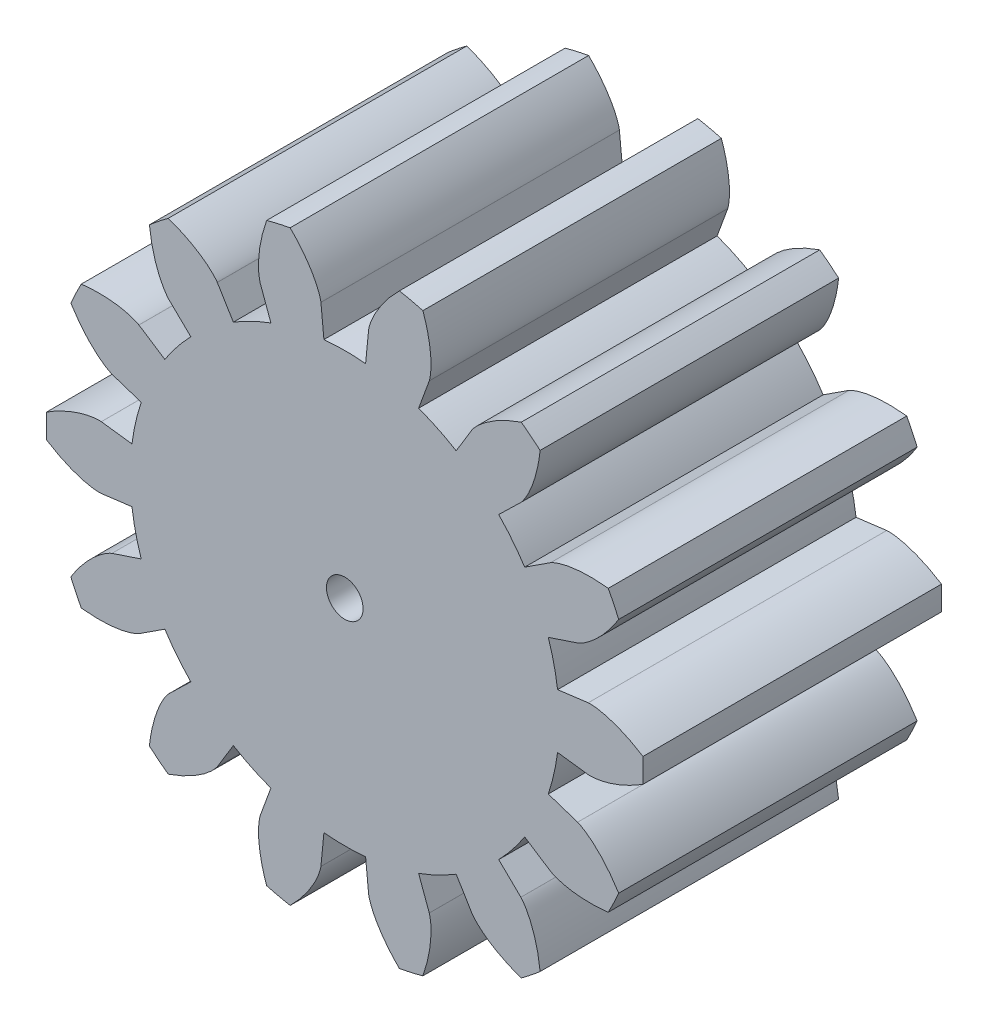
SolidWorks part; units mm, degrees
ref_plane "Front Plane" through (0, 0, 0) normal (0, 0, 1) x (1, 0, 0)
ref_plane "Top Plane" through (0, 0, 0) normal (0, 1, 0) x (1, 0, 0)
ref_plane "Right Plane" through (0, 0, 0) normal (1, 0, 0) x (0, 0, -1)
sketch "Sketch1" plane through (0, 0, 0) normal (0, 0, 1) x (1, 0, 0)
  line L0 (11.8001, -11.4535) -> (10.315, -10.012)
  line L1 (11.8013, -11.4547) -> (11.8001, -11.4535)
  line L2 (8.5406, -14.0529) -> (8.5414, -14.0543)
  line L3 (7.4657, -12.2843) -> (8.5406, -14.0529)
  line L4 (5.662, -15.4391) -> (4.9495, -13.4961)
  line L5 (5.6626, -15.4407) -> (5.662, -15.4391)
  line L6 (1.5975, -16.3668) -> (1.5976, -16.3685)
  line L7 (1.3964, -14.307) -> (1.5975, -16.3668)
  line L8 (-1.5975, -16.3668) -> (-1.3964, -14.307)
  line L9 (-1.5976, -16.3685) -> (-1.5975, -16.3668)
  line L10 (-5.662, -15.4391) -> (-5.6626, -15.4407)
  line L11 (-4.9495, -13.4961) -> (-5.662, -15.4391)
  line L12 (-8.5406, -14.0529) -> (-7.4657, -12.2843)
  line L13 (-8.5414, -14.0543) -> (-8.5406, -14.0529)
  line L14 (-11.8001, -11.4535) -> (-11.8013, -11.4547)
  line L15 (-10.315, -10.012) -> (-11.8001, -11.4535)
  line L16 (-13.7921, -8.9556) -> (-12.0563, -7.8285)
  line L17 (-13.7935, -8.9565) -> (-13.7921, -8.9556)
  line L18 (-15.601, -5.1994) -> (-15.6026, -5.1999)
  line L19 (-13.6376, -4.545) -> (-15.601, -5.1994)
  line L20 (-16.312, -2.0846) -> (-14.259, -1.8222)
  line L21 (-16.3136, -2.0847) -> (-16.312, -2.0846)
  line L22 (-16.312, 2.0846) -> (-16.3136, 2.0847)
  line L23 (-14.259, 1.8222) -> (-16.312, 2.0846)
  line L24 (-15.601, 5.1994) -> (-13.6376, 4.545)
  line L25 (-15.6026, 5.1999) -> (-15.601, 5.1994)
  line L26 (-13.7921, 8.9556) -> (-13.7935, 8.9565)
  line L27 (-12.0563, 7.8285) -> (-13.7921, 8.9556)
  line L28 (-11.8001, 11.4535) -> (-10.315, 10.012)
  line L29 (-11.8013, 11.4547) -> (-11.8001, 11.4535)
  line L30 (-8.5406, 14.0529) -> (-8.5414, 14.0543)
  line L31 (-7.4657, 12.2843) -> (-8.5406, 14.0529)
  line L32 (-5.662, 15.4391) -> (-4.9495, 13.4961)
  line L33 (-5.6626, 15.4407) -> (-5.662, 15.4391)
  line L34 (-1.5975, 16.3668) -> (-1.5976, 16.3685)
  line L35 (-1.3964, 14.307) -> (-1.5975, 16.3668)
  line L36 (1.5975, 16.3668) -> (1.3964, 14.307)
  line L37 (1.5976, 16.3685) -> (1.5975, 16.3668)
  line L38 (5.662, 15.4391) -> (5.6626, 15.4407)
  line L39 (4.9495, 13.4961) -> (5.662, 15.4391)
  line L40 (8.5406, 14.0529) -> (7.4657, 12.2843)
  line L41 (8.5414, 14.0543) -> (8.5406, 14.0529)
  line L42 (11.8001, 11.4535) -> (11.8013, 11.4547)
  line L43 (10.315, 10.012) -> (11.8001, 11.4535)
  line L44 (13.7921, 8.9556) -> (12.0563, 7.8285)
  line L45 (13.7935, 8.9565) -> (13.7921, 8.9556)
  line L46 (15.601, 5.1994) -> (15.6026, 5.1999)
  line L47 (13.6376, 4.545) -> (15.601, 5.1994)
  line L48 (16.312, 2.0846) -> (14.259, 1.8222)
  line L49 (16.3136, 2.0847) -> (16.312, 2.0846)
  line L50 (16.312, -2.0846) -> (16.3136, -2.0847)
  line L51 (14.259, -1.8222) -> (16.312, -2.0846)
  line L52 (15.601, -5.1994) -> (13.6376, -4.545)
  line L53 (15.6026, -5.1999) -> (15.601, -5.1994)
  line L54 (13.7921, -8.9556) -> (13.7935, -8.9565)
  line L55 (12.0563, -7.8285) -> (13.7921, -8.9556)
  arc A0 (10.315, -10.012) -> (12.0563, -7.8285) centre (0, 0) ccw
  arc A1 (11.8285, -16.1272) -> (13.0908, -15.1206) centre (0, 0) ccw
  arc A2 (4.9495, -13.4961) -> (7.4657, -12.2843) centre (0, 0) ccw
  arc A3 (3.6598, -19.6623) -> (5.2338, -19.303) centre (0, 0) ccw
  arc A4 (-1.3964, -14.307) -> (1.3964, -14.307) centre (0, 0) ccw
  arc A5 (-5.2338, -19.303) -> (-3.6598, -19.6623) centre (0, 0) ccw
  arc A6 (-7.4657, -12.2843) -> (-4.9495, -13.4961) centre (0, 0) ccw
  arc A7 (-13.0908, -15.1206) -> (-11.8285, -16.1272) centre (0, 0) ccw
  arc A8 (-12.0563, -7.8285) -> (-10.315, -10.012) centre (0, 0) ccw
  arc A9 (-18.3549, -7.9433) -> (-17.6544, -9.3979) centre (0, 0) ccw
  arc A10 (-14.259, -1.8222) -> (-13.6376, -4.545) centre (0, 0) ccw
  arc A11 (-19.9837, 0.8073) -> (-19.9837, -0.8073) centre (0, 0) ccw
  arc A12 (-13.6376, 4.545) -> (-14.259, 1.8222) centre (0, 0) ccw
  arc A13 (-17.6544, 9.3979) -> (-18.3549, 7.9433) centre (0, 0) ccw
  arc A14 (-10.315, 10.012) -> (-12.0563, 7.8285) centre (0, 0) ccw
  arc A15 (-11.8285, 16.1272) -> (-13.0908, 15.1206) centre (0, 0) ccw
  arc A16 (-4.9495, 13.4961) -> (-7.4657, 12.2843) centre (0, 0) ccw
  arc A17 (-3.6598, 19.6623) -> (-5.2338, 19.303) centre (0, 0) ccw
  arc A18 (1.3964, 14.307) -> (-1.3964, 14.307) centre (0, 0) ccw
  arc A19 (5.2338, 19.303) -> (3.6598, 19.6623) centre (0, 0) ccw
  arc A20 (7.4657, 12.2843) -> (4.9495, 13.4961) centre (0, 0) ccw
  arc A21 (13.0908, 15.1206) -> (11.8285, 16.1272) centre (0, 0) ccw
  arc A22 (12.0563, 7.8285) -> (10.315, 10.012) centre (0, 0) ccw
  arc A23 (18.3549, 7.9433) -> (17.6544, 9.3979) centre (0, 0) ccw
  arc A24 (14.259, 1.8222) -> (13.6376, 4.545) centre (0, 0) ccw
  arc A25 (19.9837, -0.8073) -> (19.9837, 0.8073) centre (0, 0) ccw
  arc A26 (13.6376, -4.545) -> (14.259, -1.8222) centre (0, 0) ccw
  arc A27 (17.6544, -9.3979) -> (18.3549, -7.9433) centre (0, 0) ccw
  circle A28 centre (0, 0) radius 1.2268
  spline S0 degree 5 poles (13.0908, -15.1206) (13.0892, -15.1057) (13.0837, -15.0564) (13.0741, -14.9729) (13.0534, -14.8076) (13.0196, -14.5739) (12.9712, -14.2913) (12.9095, -13.9876) (12.8326, -13.6678) (12.7526, -13.3794) (12.6689, -13.1136) (12.5842, -12.8734) (12.5, -12.6578) (12.4177, -12.4654) (12.3382, -12.2951) (12.264, -12.1481) (12.1946, -12.0199) (12.1305, -11.9094) (12.0722, -11.8149) (12.02, -11.7352) (11.9742, -11.669) (11.9347, -11.6148) (11.9014, -11.5712) (11.8749, -11.5382) (11.8529, -11.5117) (11.836, -11.4921) (11.824, -11.4787) (11.8135, -11.4673) (11.8071, -11.4606) (11.8039, -11.4573) (11.8022, -11.4556) (11.8013, -11.4547) knots 0 0 0 0 0 0 0.0125 0.041667 0.070833 0.141667 0.204167 0.266667 0.325 0.383333 0.4375 0.491667 0.541667 0.5875 0.633333 0.675 0.7125 0.75 0.783333 0.816667 0.845833 0.870833 0.895833 0.916667 0.933333 0.954167 0.966667 0.975 1 1 1 1 1 1 weights 1 1 1 1 1 1 1 1 1 1 1 1 1 1 1 1 1 1 1 1 1 1 1 1 1 1 1 1 1 1 1 1
  spline S1 degree 5 poles (8.5414, -14.0543) (8.5418, -14.0548) (8.5426, -14.0561) (8.5443, -14.0588) (8.5474, -14.0636) (8.5539, -14.0732) (8.5633, -14.0868) (8.5824, -14.1133) (8.6247, -14.1691) (8.699, -14.2586) (8.8131, -14.3827) (8.9784, -14.5426) (9.1766, -14.7141) (9.3765, -14.8717) (9.593, -15.028) (9.8169, -15.1767) (10.0477, -15.3185) (10.2796, -15.4503) (10.5206, -15.5776) (10.7579, -15.694) (10.9807, -15.7959) (11.237, -15.9058) (11.4544, -15.992) (11.6185, -16.0533) (11.7392, -16.0964) (11.8285, -16.1272) knots 0 0 0 0 0 0 0.0125 0.025 0.0375 0.05 0.075 0.095833 0.158333 0.258333 0.325 0.395833 0.4625 0.525 0.583333 0.641667 0.695833 0.75 0.795833 0.85 0.891667 0.920833 1 1 1 1 1 1 weights 1 1 1 1 1 1 1 1 1 1 1 1 1 1 1 1 1 1 1 1 1 1 1 1 1 1
  spline S2 degree 5 poles (5.2338, -19.303) (5.2388, -19.289) (5.2553, -19.2421) (5.2828, -19.1628) (5.3359, -19.0048) (5.4069, -18.7797) (5.4859, -18.504) (5.5621, -18.2036) (5.6315, -17.8821) (5.6845, -17.5876) (5.7245, -17.3118) (5.7524, -17.0587) (5.7701, -16.8279) (5.7794, -16.6188) (5.7817, -16.4308) (5.7787, -16.2662) (5.7717, -16.1206) (5.7619, -15.9932) (5.7504, -15.8827) (5.738, -15.7883) (5.7254, -15.7088) (5.7133, -15.6428) (5.7022, -15.5891) (5.6927, -15.5479) (5.6844, -15.5145) (5.6776, -15.4895) (5.6726, -15.4722) (5.6681, -15.4574) (5.6653, -15.4486) (5.6638, -15.4442) (5.663, -15.4419) (5.6626, -15.4407) knots 0 0 0 0 0 0 0.0125 0.041667 0.070833 0.141667 0.204167 0.266667 0.325 0.383333 0.4375 0.491667 0.541667 0.5875 0.633333 0.675 0.7125 0.75 0.783333 0.816667 0.845833 0.870833 0.895833 0.916667 0.933333 0.954167 0.966667 0.975 1 1 1 1 1 1 weights 1 1 1 1 1 1 1 1 1 1 1 1 1 1 1 1 1 1 1 1 1 1 1 1 1 1 1 1 1 1 1 1
  spline S3 degree 5 poles (1.5976, -16.3685) (1.5977, -16.3691) (1.5979, -16.3706) (1.5983, -16.3737) (1.599, -16.3795) (1.6006, -16.3909) (1.6032, -16.4072) (1.6089, -16.4394) (1.6229, -16.508) (1.6509, -16.621) (1.6999, -16.7823) (1.7795, -16.998) (1.8836, -17.2385) (1.9953, -17.4672) (2.1226, -17.702) (2.2598, -17.9331) (2.4063, -18.161) (2.558, -18.3804) (2.7199, -18.5996) (2.8831, -18.8075) (3.0397, -18.9959) (3.2229, -19.2061) (3.3814, -19.3782) (3.5027, -19.5046) (3.5927, -19.5957) (3.6598, -19.6623) knots 0 0 0 0 0 0 0.0125 0.025 0.0375 0.05 0.075 0.095833 0.158333 0.258333 0.325 0.395833 0.4625 0.525 0.583333 0.641667 0.695833 0.75 0.795833 0.85 0.891667 0.920833 1 1 1 1 1 1 weights 1 1 1 1 1 1 1 1 1 1 1 1 1 1 1 1 1 1 1 1 1 1 1 1 1 1
  spline S4 degree 5 poles (-3.6598, -19.6623) (-3.6492, -19.6518) (-3.614, -19.6168) (-3.5548, -19.5572) (-3.4384, -19.4379) (-3.2768, -19.2658) (-3.086, -19.0518) (-2.887, -18.8142) (-2.6849, -18.5546) (-2.5094, -18.3123) (-2.3537, -18.0811) (-2.2187, -17.8652) (-2.1026, -17.6649) (-2.0036, -17.4806) (-1.9199, -17.3122) (-1.8512, -17.1626) (-1.7944, -17.0284) (-1.7479, -16.9094) (-1.7104, -16.8049) (-1.6806, -16.7144) (-1.6574, -16.6373) (-1.6396, -16.5726) (-1.6264, -16.5194) (-1.617, -16.4781) (-1.61, -16.4444) (-1.6053, -16.419) (-1.6023, -16.4013) (-1.5999, -16.3859) (-1.5986, -16.3767) (-1.5981, -16.3721) (-1.5978, -16.3697) (-1.5976, -16.3685) knots 0 0 0 0 0 0 0.0125 0.041667 0.070833 0.141667 0.204167 0.266667 0.325 0.383333 0.4375 0.491667 0.541667 0.5875 0.633333 0.675 0.7125 0.75 0.783333 0.816667 0.845833 0.870833 0.895833 0.916667 0.933333 0.954167 0.966667 0.975 1 1 1 1 1 1 weights 1 1 1 1 1 1 1 1 1 1 1 1 1 1 1 1 1 1 1 1 1 1 1 1 1 1 1 1 1 1 1 1
  spline S5 degree 5 poles (-5.6626, -15.4407) (-5.6628, -15.4413) (-5.6633, -15.4427) (-5.6643, -15.4457) (-5.6661, -15.4512) (-5.6696, -15.4622) (-5.6744, -15.478) (-5.6832, -15.5095) (-5.7004, -15.5773) (-5.7241, -15.6913) (-5.75, -15.8579) (-5.7719, -16.0868) (-5.7824, -16.3486) (-5.781, -16.6032) (-5.7682, -16.8699) (-5.7449, -17.1377) (-5.7118, -17.4065) (-5.6703, -17.67) (-5.6196, -17.9378) (-5.5627, -18.1959) (-5.5034, -18.4336) (-5.4295, -18.7025) (-5.3613, -18.9263) (-5.3069, -19.0928) (-5.2654, -19.214) (-5.2338, -19.303) knots 0 0 0 0 0 0 0.0125 0.025 0.0375 0.05 0.075 0.095833 0.158333 0.258333 0.325 0.395833 0.4625 0.525 0.583333 0.641667 0.695833 0.75 0.795833 0.85 0.891667 0.920833 1 1 1 1 1 1 weights 1 1 1 1 1 1 1 1 1 1 1 1 1 1 1 1 1 1 1 1 1 1 1 1 1 1
  spline S6 degree 5 poles (-11.8285, -16.1272) (-11.8144, -16.1223) (-11.7675, -16.106) (-11.6883, -16.0781) (-11.5317, -16.0211) (-11.3114, -15.9362) (-11.0466, -15.8261) (-10.7643, -15.6984) (-10.4696, -15.5522) (-10.2063, -15.41) (-9.9657, -15.2693) (-9.7504, -15.1333) (-9.5589, -15.0033) (-9.3897, -14.8801) (-9.2413, -14.7647) (-9.1145, -14.6597) (-9.005, -14.5635) (-8.9115, -14.4764) (-8.8323, -14.3985) (-8.7663, -14.33) (-8.7119, -14.2705) (-8.6678, -14.22) (-8.6328, -14.1778) (-8.6064, -14.1447) (-8.5855, -14.1173) (-8.5702, -14.0965) (-8.5599, -14.0818) (-8.551, -14.069) (-8.5459, -14.0613) (-8.5434, -14.0574) (-8.5421, -14.0554) (-8.5414, -14.0543) knots 0 0 0 0 0 0 0.0125 0.041667 0.070833 0.141667 0.204167 0.266667 0.325 0.383333 0.4375 0.491667 0.541667 0.5875 0.633333 0.675 0.7125 0.75 0.783333 0.816667 0.845833 0.870833 0.895833 0.916667 0.933333 0.954167 0.966667 0.975 1 1 1 1 1 1 weights 1 1 1 1 1 1 1 1 1 1 1 1 1 1 1 1 1 1 1 1 1 1 1 1 1 1 1 1 1 1 1 1
  spline S7 degree 5 poles (-11.8013, -11.4547) (-11.8017, -11.4551) (-11.8028, -11.4562) (-11.805, -11.4584) (-11.809, -11.4626) (-11.8169, -11.471) (-11.8281, -11.4832) (-11.8497, -11.5077) (-11.8946, -11.5614) (-11.9654, -11.6537) (-12.061, -11.7926) (-12.1801, -11.9894) (-12.3032, -12.2207) (-12.4124, -12.4507) (-12.5165, -12.6965) (-12.6117, -12.9479) (-12.6986, -13.2045) (-12.7755, -13.4598) (-12.8459, -13.7231) (-12.9067, -13.9804) (-12.9564, -14.2203) (-13.0065, -14.4946) (-13.0422, -14.7258) (-13.0654, -14.8994) (-13.0806, -15.0266) (-13.0908, -15.1206) knots 0 0 0 0 0 0 0.0125 0.025 0.0375 0.05 0.075 0.095833 0.158333 0.258333 0.325 0.395833 0.4625 0.525 0.583333 0.641667 0.695833 0.75 0.795833 0.85 0.891667 0.920833 1 1 1 1 1 1 weights 1 1 1 1 1 1 1 1 1 1 1 1 1 1 1 1 1 1 1 1 1 1 1 1 1 1
  spline S8 degree 5 poles (-17.6544, -9.3979) (-17.6396, -9.3996) (-17.5903, -9.4053) (-17.5068, -9.4145) (-17.341, -9.4311) (-17.1057, -9.4502) (-16.8194, -9.4659) (-16.5096, -9.4733) (-16.1806, -9.4695) (-15.8817, -9.4556) (-15.6039, -9.4332) (-15.3509, -9.4041) (-15.122, -9.37) (-14.9161, -9.3325) (-14.7323, -9.2929) (-14.5725, -9.2533) (-14.4321, -9.2141) (-14.3101, -9.1763) (-14.205, -9.1404) (-14.1157, -9.1073) (-14.0409, -9.0774) (-13.9793, -9.0509) (-13.9294, -9.0281) (-13.8913, -9.0097) (-13.8606, -8.9941) (-13.8377, -8.982) (-13.822, -8.9733) (-13.8085, -8.9656) (-13.8006, -8.9609) (-13.7966, -8.9584) (-13.7946, -8.9572) (-13.7935, -8.9565) knots 0 0 0 0 0 0 0.0125 0.041667 0.070833 0.141667 0.204167 0.266667 0.325 0.383333 0.4375 0.491667 0.541667 0.5875 0.633333 0.675 0.7125 0.75 0.783333 0.816667 0.845833 0.870833 0.895833 0.916667 0.933333 0.954167 0.966667 0.975 1 1 1 1 1 1 weights 1 1 1 1 1 1 1 1 1 1 1 1 1 1 1 1 1 1 1 1 1 1 1 1 1 1 1 1 1 1 1 1
  spline S9 degree 5 poles (-15.6026, -5.1999) (-15.6032, -5.2001) (-15.6046, -5.2006) (-15.6076, -5.2017) (-15.613, -5.2037) (-15.6237, -5.2078) (-15.6391, -5.214) (-15.6692, -5.2267) (-15.733, -5.2556) (-15.8369, -5.308) (-15.9832, -5.3917) (-16.1759, -5.5173) (-16.3871, -5.6723) (-16.5853, -5.8321) (-16.7858, -6.0084) (-16.9807, -6.1936) (-17.1702, -6.3872) (-17.3503, -6.5838) (-17.528, -6.7905) (-17.6944, -6.9959) (-17.8433, -7.1905) (-18.0074, -7.4159) (-18.1399, -7.6087) (-18.2362, -7.755) (-18.305, -7.8631) (-18.3549, -7.9433) knots 0 0 0 0 0 0 0.0125 0.025 0.0375 0.05 0.075 0.095833 0.158333 0.258333 0.325 0.395833 0.4625 0.525 0.583333 0.641667 0.695833 0.75 0.795833 0.85 0.891667 0.920833 1 1 1 1 1 1 weights 1 1 1 1 1 1 1 1 1 1 1 1 1 1 1 1 1 1 1 1 1 1 1 1 1 1
  spline S10 degree 5 poles (-19.9837, -0.8073) (-19.9711, -0.8152) (-19.9291, -0.8418) (-19.8578, -0.8863) (-19.7157, -0.9732) (-19.512, -1.0924) (-19.2608, -1.2308) (-18.9849, -1.3719) (-18.6868, -1.5112) (-18.4116, -1.6284) (-18.1516, -1.7287) (-17.911, -1.8123) (-17.6899, -1.8809) (-17.4881, -1.9364) (-17.3054, -1.9805) (-17.1442, -2.0142) (-17.0007, -2.0398) (-16.8744, -2.0586) (-16.7641, -2.0719) (-16.6693, -2.0809) (-16.5889, -2.0863) (-16.5219, -2.0892) (-16.4671, -2.0903) (-16.4248, -2.0903) (-16.3904, -2.0896) (-16.3645, -2.0885) (-16.3466, -2.0875) (-16.3311, -2.0864) (-16.3219, -2.0856) (-16.3173, -2.0852) (-16.3149, -2.0849) (-16.3136, -2.0847) knots 0 0 0 0 0 0 0.0125 0.041667 0.070833 0.141667 0.204167 0.266667 0.325 0.383333 0.4375 0.491667 0.541667 0.5875 0.633333 0.675 0.7125 0.75 0.783333 0.816667 0.845833 0.870833 0.895833 0.916667 0.933333 0.954167 0.966667 0.975 1 1 1 1 1 1 weights 1 1 1 1 1 1 1 1 1 1 1 1 1 1 1 1 1 1 1 1 1 1 1 1 1 1 1 1 1 1 1 1
  spline S11 degree 5 poles (-16.3136, 2.0847) (-16.3142, 2.0848) (-16.3158, 2.085) (-16.3189, 2.0853) (-16.3246, 2.0859) (-16.3361, 2.0868) (-16.3526, 2.0879) (-16.3852, 2.0895) (-16.4552, 2.0912) (-16.5716, 2.089) (-16.7398, 2.0771) (-16.9678, 2.0475) (-17.2254, 1.9995) (-17.4733, 1.9415) (-17.7305, 1.8697) (-17.9864, 1.7874) (-18.2411, 1.6953) (-18.4887, 1.5962) (-18.7385, 1.4871) (-18.9775, 1.3742) (-19.196, 1.2635) (-19.4418, 1.1317) (-19.6448, 1.0154) (-19.795, 0.9253) (-19.9039, 0.8579) (-19.9837, 0.8073) knots 0 0 0 0 0 0 0.0125 0.025 0.0375 0.05 0.075 0.095833 0.158333 0.258333 0.325 0.395833 0.4625 0.525 0.583333 0.641667 0.695833 0.75 0.795833 0.85 0.891667 0.920833 1 1 1 1 1 1 weights 1 1 1 1 1 1 1 1 1 1 1 1 1 1 1 1 1 1 1 1 1 1 1 1 1 1
  spline S12 degree 5 poles (-18.3549, 7.9433) (-18.3471, 7.9306) (-18.3207, 7.8885) (-18.2758, 7.8175) (-18.1854, 7.6775) (-18.0536, 7.4817) (-17.8874, 7.248) (-17.7001, 7.0012) (-17.4919, 6.7464) (-17.2948, 6.5213) (-17.104, 6.3181) (-16.9236, 6.1385) (-16.7542, 5.9807) (-16.5965, 5.8431) (-16.4509, 5.7241) (-16.3204, 5.6239) (-16.2022, 5.5385) (-16.0965, 5.4668) (-16.0029, 5.4069) (-15.9214, 5.3577) (-15.8513, 5.318) (-15.7922, 5.2863) (-15.7433, 5.2615) (-15.7052, 5.2432) (-15.6738, 5.2289) (-15.6501, 5.2186) (-15.6335, 5.2117) (-15.6191, 5.206) (-15.6104, 5.2027) (-15.606, 5.2011) (-15.6038, 5.2003) (-15.6026, 5.1999) knots 0 0 0 0 0 0 0.0125 0.041667 0.070833 0.141667 0.204167 0.266667 0.325 0.383333 0.4375 0.491667 0.541667 0.5875 0.633333 0.675 0.7125 0.75 0.783333 0.816667 0.845833 0.870833 0.895833 0.916667 0.933333 0.954167 0.966667 0.975 1 1 1 1 1 1 weights 1 1 1 1 1 1 1 1 1 1 1 1 1 1 1 1 1 1 1 1 1 1 1 1 1 1 1 1 1 1 1 1
  spline S13 degree 5 poles (-13.7935, 8.9565) (-13.794, 8.9568) (-13.7953, 8.9577) (-13.798, 8.9593) (-13.8029, 8.9623) (-13.8129, 8.9681) (-13.8273, 8.9763) (-13.856, 8.9919) (-13.9183, 9.0238) (-14.0241, 9.0722) (-14.1808, 9.1345) (-14.3991, 9.2068) (-14.652, 9.2753) (-14.9005, 9.3306) (-15.1634, 9.3775) (-15.4296, 9.4144) (-15.6991, 9.4419) (-15.9652, 9.4601) (-16.2376, 9.4702) (-16.5019, 9.4722) (-16.7468, 9.4672) (-17.0254, 9.4551) (-17.2588, 9.4384) (-17.4332, 9.4224) (-17.5606, 9.4089) (-17.6544, 9.3979) knots 0 0 0 0 0 0 0.0125 0.025 0.0375 0.05 0.075 0.095833 0.158333 0.258333 0.325 0.395833 0.4625 0.525 0.583333 0.641667 0.695833 0.75 0.795833 0.85 0.891667 0.920833 1 1 1 1 1 1 weights 1 1 1 1 1 1 1 1 1 1 1 1 1 1 1 1 1 1 1 1 1 1 1 1 1 1
  spline S14 degree 5 poles (-13.0908, 15.1206) (-13.0892, 15.1057) (-13.0837, 15.0564) (-13.0741, 14.9729) (-13.0534, 14.8076) (-13.0196, 14.5739) (-12.9712, 14.2913) (-12.9095, 13.9876) (-12.8326, 13.6678) (-12.7526, 13.3794) (-12.6689, 13.1136) (-12.5842, 12.8734) (-12.5, 12.6578) (-12.4177, 12.4654) (-12.3382, 12.2951) (-12.264, 12.1481) (-12.1946, 12.0199) (-12.1305, 11.9094) (-12.0722, 11.8149) (-12.02, 11.7352) (-11.9742, 11.669) (-11.9347, 11.6148) (-11.9014, 11.5712) (-11.8749, 11.5382) (-11.8529, 11.5117) (-11.836, 11.4921) (-11.824, 11.4787) (-11.8135, 11.4673) (-11.8071, 11.4606) (-11.8039, 11.4573) (-11.8022, 11.4556) (-11.8013, 11.4547) knots 0 0 0 0 0 0 0.0125 0.041667 0.070833 0.141667 0.204167 0.266667 0.325 0.383333 0.4375 0.491667 0.541667 0.5875 0.633333 0.675 0.7125 0.75 0.783333 0.816667 0.845833 0.870833 0.895833 0.916667 0.933333 0.954167 0.966667 0.975 1 1 1 1 1 1 weights 1 1 1 1 1 1 1 1 1 1 1 1 1 1 1 1 1 1 1 1 1 1 1 1 1 1 1 1 1 1 1 1
  spline S15 degree 5 poles (-8.5414, 14.0543) (-8.5418, 14.0548) (-8.5426, 14.0561) (-8.5443, 14.0588) (-8.5474, 14.0636) (-8.5539, 14.0732) (-8.5633, 14.0868) (-8.5824, 14.1133) (-8.6247, 14.1691) (-8.699, 14.2586) (-8.8131, 14.3827) (-8.9784, 14.5426) (-9.1766, 14.7141) (-9.3765, 14.8717) (-9.593, 15.028) (-9.8169, 15.1767) (-10.0477, 15.3185) (-10.2796, 15.4503) (-10.5206, 15.5776) (-10.7579, 15.694) (-10.9807, 15.7959) (-11.237, 15.9058) (-11.4544, 15.992) (-11.6185, 16.0533) (-11.7392, 16.0964) (-11.8285, 16.1272) knots 0 0 0 0 0 0 0.0125 0.025 0.0375 0.05 0.075 0.095833 0.158333 0.258333 0.325 0.395833 0.4625 0.525 0.583333 0.641667 0.695833 0.75 0.795833 0.85 0.891667 0.920833 1 1 1 1 1 1 weights 1 1 1 1 1 1 1 1 1 1 1 1 1 1 1 1 1 1 1 1 1 1 1 1 1 1
  spline S16 degree 5 poles (-5.2338, 19.303) (-5.2388, 19.289) (-5.2553, 19.2421) (-5.2828, 19.1628) (-5.3359, 19.0048) (-5.4069, 18.7797) (-5.4859, 18.504) (-5.5621, 18.2036) (-5.6315, 17.8821) (-5.6845, 17.5876) (-5.7245, 17.3118) (-5.7524, 17.0587) (-5.7701, 16.8279) (-5.7794, 16.6188) (-5.7817, 16.4308) (-5.7787, 16.2662) (-5.7717, 16.1206) (-5.7619, 15.9932) (-5.7504, 15.8827) (-5.738, 15.7883) (-5.7254, 15.7088) (-5.7133, 15.6428) (-5.7022, 15.5891) (-5.6927, 15.5479) (-5.6844, 15.5145) (-5.6776, 15.4895) (-5.6726, 15.4722) (-5.6681, 15.4574) (-5.6653, 15.4486) (-5.6638, 15.4442) (-5.663, 15.4419) (-5.6626, 15.4407) knots 0 0 0 0 0 0 0.0125 0.041667 0.070833 0.141667 0.204167 0.266667 0.325 0.383333 0.4375 0.491667 0.541667 0.5875 0.633333 0.675 0.7125 0.75 0.783333 0.816667 0.845833 0.870833 0.895833 0.916667 0.933333 0.954167 0.966667 0.975 1 1 1 1 1 1 weights 1 1 1 1 1 1 1 1 1 1 1 1 1 1 1 1 1 1 1 1 1 1 1 1 1 1 1 1 1 1 1 1
  spline S17 degree 5 poles (-1.5976, 16.3685) (-1.5977, 16.3691) (-1.5979, 16.3706) (-1.5983, 16.3737) (-1.599, 16.3795) (-1.6006, 16.3909) (-1.6032, 16.4072) (-1.6089, 16.4394) (-1.6229, 16.508) (-1.6509, 16.621) (-1.6999, 16.7823) (-1.7795, 16.998) (-1.8836, 17.2385) (-1.9953, 17.4672) (-2.1226, 17.702) (-2.2598, 17.9331) (-2.4063, 18.161) (-2.558, 18.3804) (-2.7199, 18.5996) (-2.8831, 18.8075) (-3.0397, 18.9959) (-3.2229, 19.2061) (-3.3814, 19.3782) (-3.5027, 19.5046) (-3.5927, 19.5957) (-3.6598, 19.6623) knots 0 0 0 0 0 0 0.0125 0.025 0.0375 0.05 0.075 0.095833 0.158333 0.258333 0.325 0.395833 0.4625 0.525 0.583333 0.641667 0.695833 0.75 0.795833 0.85 0.891667 0.920833 1 1 1 1 1 1 weights 1 1 1 1 1 1 1 1 1 1 1 1 1 1 1 1 1 1 1 1 1 1 1 1 1 1
  spline S18 degree 5 poles (3.6598, 19.6623) (3.6492, 19.6518) (3.614, 19.6168) (3.5548, 19.5572) (3.4384, 19.4379) (3.2768, 19.2658) (3.086, 19.0518) (2.887, 18.8142) (2.6849, 18.5546) (2.5094, 18.3123) (2.3537, 18.0811) (2.2187, 17.8652) (2.1026, 17.6649) (2.0036, 17.4806) (1.9199, 17.3122) (1.8512, 17.1626) (1.7944, 17.0284) (1.7479, 16.9094) (1.7104, 16.8049) (1.6806, 16.7144) (1.6574, 16.6373) (1.6396, 16.5726) (1.6264, 16.5194) (1.617, 16.4781) (1.61, 16.4444) (1.6053, 16.419) (1.6023, 16.4013) (1.5999, 16.3859) (1.5986, 16.3767) (1.5981, 16.3721) (1.5978, 16.3697) (1.5976, 16.3685) knots 0 0 0 0 0 0 0.0125 0.041667 0.070833 0.141667 0.204167 0.266667 0.325 0.383333 0.4375 0.491667 0.541667 0.5875 0.633333 0.675 0.7125 0.75 0.783333 0.816667 0.845833 0.870833 0.895833 0.916667 0.933333 0.954167 0.966667 0.975 1 1 1 1 1 1 weights 1 1 1 1 1 1 1 1 1 1 1 1 1 1 1 1 1 1 1 1 1 1 1 1 1 1 1 1 1 1 1 1
  spline S19 degree 5 poles (5.6626, 15.4407) (5.6628, 15.4413) (5.6633, 15.4427) (5.6643, 15.4457) (5.6661, 15.4512) (5.6696, 15.4622) (5.6744, 15.478) (5.6832, 15.5095) (5.7004, 15.5773) (5.7241, 15.6913) (5.75, 15.8579) (5.7719, 16.0868) (5.7824, 16.3486) (5.781, 16.6032) (5.7682, 16.8699) (5.7449, 17.1377) (5.7118, 17.4065) (5.6703, 17.67) (5.6196, 17.9378) (5.5627, 18.1959) (5.5034, 18.4336) (5.4295, 18.7025) (5.3613, 18.9263) (5.3069, 19.0928) (5.2654, 19.214) (5.2338, 19.303) knots 0 0 0 0 0 0 0.0125 0.025 0.0375 0.05 0.075 0.095833 0.158333 0.258333 0.325 0.395833 0.4625 0.525 0.583333 0.641667 0.695833 0.75 0.795833 0.85 0.891667 0.920833 1 1 1 1 1 1 weights 1 1 1 1 1 1 1 1 1 1 1 1 1 1 1 1 1 1 1 1 1 1 1 1 1 1
  spline S20 degree 5 poles (11.8285, 16.1272) (11.8144, 16.1223) (11.7675, 16.106) (11.6883, 16.0781) (11.5317, 16.0211) (11.3114, 15.9362) (11.0466, 15.8261) (10.7643, 15.6984) (10.4696, 15.5522) (10.2063, 15.41) (9.9657, 15.2693) (9.7504, 15.1333) (9.5589, 15.0033) (9.3897, 14.8801) (9.2413, 14.7647) (9.1145, 14.6597) (9.005, 14.5635) (8.9115, 14.4764) (8.8323, 14.3985) (8.7663, 14.33) (8.7119, 14.2705) (8.6678, 14.22) (8.6328, 14.1778) (8.6064, 14.1447) (8.5855, 14.1173) (8.5702, 14.0965) (8.5599, 14.0818) (8.551, 14.069) (8.5459, 14.0613) (8.5434, 14.0574) (8.5421, 14.0554) (8.5414, 14.0543) knots 0 0 0 0 0 0 0.0125 0.041667 0.070833 0.141667 0.204167 0.266667 0.325 0.383333 0.4375 0.491667 0.541667 0.5875 0.633333 0.675 0.7125 0.75 0.783333 0.816667 0.845833 0.870833 0.895833 0.916667 0.933333 0.954167 0.966667 0.975 1 1 1 1 1 1 weights 1 1 1 1 1 1 1 1 1 1 1 1 1 1 1 1 1 1 1 1 1 1 1 1 1 1 1 1 1 1 1 1
  spline S21 degree 5 poles (11.8013, 11.4547) (11.8017, 11.4551) (11.8028, 11.4562) (11.805, 11.4584) (11.809, 11.4626) (11.8169, 11.471) (11.8281, 11.4832) (11.8497, 11.5077) (11.8946, 11.5614) (11.9654, 11.6537) (12.061, 11.7926) (12.1801, 11.9894) (12.3032, 12.2207) (12.4124, 12.4507) (12.5165, 12.6965) (12.6117, 12.9479) (12.6986, 13.2045) (12.7755, 13.4598) (12.8459, 13.7231) (12.9067, 13.9804) (12.9564, 14.2203) (13.0065, 14.4946) (13.0422, 14.7258) (13.0654, 14.8994) (13.0806, 15.0266) (13.0908, 15.1206) knots 0 0 0 0 0 0 0.0125 0.025 0.0375 0.05 0.075 0.095833 0.158333 0.258333 0.325 0.395833 0.4625 0.525 0.583333 0.641667 0.695833 0.75 0.795833 0.85 0.891667 0.920833 1 1 1 1 1 1 weights 1 1 1 1 1 1 1 1 1 1 1 1 1 1 1 1 1 1 1 1 1 1 1 1 1 1
  spline S22 degree 5 poles (17.6544, 9.3979) (17.6396, 9.3996) (17.5903, 9.4053) (17.5068, 9.4145) (17.341, 9.4311) (17.1057, 9.4502) (16.8194, 9.4659) (16.5096, 9.4733) (16.1806, 9.4695) (15.8817, 9.4556) (15.6039, 9.4332) (15.3509, 9.4041) (15.122, 9.37) (14.9161, 9.3325) (14.7323, 9.2929) (14.5725, 9.2533) (14.4321, 9.2141) (14.3101, 9.1763) (14.205, 9.1404) (14.1157, 9.1073) (14.0409, 9.0774) (13.9793, 9.0509) (13.9294, 9.0281) (13.8913, 9.0097) (13.8606, 8.9941) (13.8377, 8.982) (13.822, 8.9733) (13.8085, 8.9656) (13.8006, 8.9609) (13.7966, 8.9584) (13.7946, 8.9572) (13.7935, 8.9565) knots 0 0 0 0 0 0 0.0125 0.041667 0.070833 0.141667 0.204167 0.266667 0.325 0.383333 0.4375 0.491667 0.541667 0.5875 0.633333 0.675 0.7125 0.75 0.783333 0.816667 0.845833 0.870833 0.895833 0.916667 0.933333 0.954167 0.966667 0.975 1 1 1 1 1 1 weights 1 1 1 1 1 1 1 1 1 1 1 1 1 1 1 1 1 1 1 1 1 1 1 1 1 1 1 1 1 1 1 1
  spline S23 degree 5 poles (15.6026, 5.1999) (15.6032, 5.2001) (15.6046, 5.2006) (15.6076, 5.2017) (15.613, 5.2037) (15.6237, 5.2078) (15.6391, 5.214) (15.6692, 5.2267) (15.733, 5.2556) (15.8369, 5.308) (15.9832, 5.3917) (16.1759, 5.5173) (16.3871, 5.6723) (16.5853, 5.8321) (16.7858, 6.0084) (16.9807, 6.1936) (17.1702, 6.3872) (17.3503, 6.5838) (17.528, 6.7905) (17.6944, 6.9959) (17.8433, 7.1905) (18.0074, 7.4159) (18.1399, 7.6087) (18.2362, 7.755) (18.305, 7.8631) (18.3549, 7.9433) knots 0 0 0 0 0 0 0.0125 0.025 0.0375 0.05 0.075 0.095833 0.158333 0.258333 0.325 0.395833 0.4625 0.525 0.583333 0.641667 0.695833 0.75 0.795833 0.85 0.891667 0.920833 1 1 1 1 1 1 weights 1 1 1 1 1 1 1 1 1 1 1 1 1 1 1 1 1 1 1 1 1 1 1 1 1 1
  spline S24 degree 5 poles (19.9837, 0.8073) (19.9711, 0.8152) (19.9291, 0.8418) (19.8578, 0.8863) (19.7157, 0.9732) (19.512, 1.0924) (19.2608, 1.2308) (18.9849, 1.3719) (18.6868, 1.5112) (18.4116, 1.6284) (18.1516, 1.7287) (17.911, 1.8123) (17.6899, 1.8809) (17.4881, 1.9364) (17.3054, 1.9805) (17.1442, 2.0142) (17.0007, 2.0398) (16.8744, 2.0586) (16.7641, 2.0719) (16.6693, 2.0809) (16.5889, 2.0863) (16.5219, 2.0892) (16.4671, 2.0903) (16.4248, 2.0903) (16.3904, 2.0896) (16.3645, 2.0885) (16.3466, 2.0875) (16.3311, 2.0864) (16.3219, 2.0856) (16.3173, 2.0852) (16.3149, 2.0849) (16.3136, 2.0847) knots 0 0 0 0 0 0 0.0125 0.041667 0.070833 0.141667 0.204167 0.266667 0.325 0.383333 0.4375 0.491667 0.541667 0.5875 0.633333 0.675 0.7125 0.75 0.783333 0.816667 0.845833 0.870833 0.895833 0.916667 0.933333 0.954167 0.966667 0.975 1 1 1 1 1 1 weights 1 1 1 1 1 1 1 1 1 1 1 1 1 1 1 1 1 1 1 1 1 1 1 1 1 1 1 1 1 1 1 1
  spline S25 degree 5 poles (16.3136, -2.0847) (16.3142, -2.0848) (16.3158, -2.085) (16.3189, -2.0853) (16.3246, -2.0859) (16.3361, -2.0868) (16.3526, -2.0879) (16.3852, -2.0895) (16.4552, -2.0912) (16.5716, -2.089) (16.7398, -2.0771) (16.9678, -2.0475) (17.2254, -1.9995) (17.4733, -1.9415) (17.7305, -1.8697) (17.9864, -1.7874) (18.2411, -1.6953) (18.4887, -1.5962) (18.7385, -1.4871) (18.9775, -1.3742) (19.196, -1.2635) (19.4418, -1.1317) (19.6448, -1.0154) (19.795, -0.9253) (19.9039, -0.8579) (19.9837, -0.8073) knots 0 0 0 0 0 0 0.0125 0.025 0.0375 0.05 0.075 0.095833 0.158333 0.258333 0.325 0.395833 0.4625 0.525 0.583333 0.641667 0.695833 0.75 0.795833 0.85 0.891667 0.920833 1 1 1 1 1 1 weights 1 1 1 1 1 1 1 1 1 1 1 1 1 1 1 1 1 1 1 1 1 1 1 1 1 1
  spline S26 degree 5 poles (18.3549, -7.9433) (18.3471, -7.9306) (18.3207, -7.8885) (18.2758, -7.8175) (18.1854, -7.6775) (18.0536, -7.4817) (17.8874, -7.248) (17.7001, -7.0012) (17.4919, -6.7464) (17.2948, -6.5213) (17.104, -6.3181) (16.9236, -6.1385) (16.7542, -5.9807) (16.5965, -5.8431) (16.4509, -5.7241) (16.3204, -5.6239) (16.2022, -5.5385) (16.0965, -5.4668) (16.0029, -5.4069) (15.9214, -5.3577) (15.8513, -5.318) (15.7922, -5.2863) (15.7433, -5.2615) (15.7052, -5.2432) (15.6738, -5.2289) (15.6501, -5.2186) (15.6335, -5.2117) (15.6191, -5.206) (15.6104, -5.2027) (15.606, -5.2011) (15.6038, -5.2003) (15.6026, -5.1999) knots 0 0 0 0 0 0 0.0125 0.041667 0.070833 0.141667 0.204167 0.266667 0.325 0.383333 0.4375 0.491667 0.541667 0.5875 0.633333 0.675 0.7125 0.75 0.783333 0.816667 0.845833 0.870833 0.895833 0.916667 0.933333 0.954167 0.966667 0.975 1 1 1 1 1 1 weights 1 1 1 1 1 1 1 1 1 1 1 1 1 1 1 1 1 1 1 1 1 1 1 1 1 1 1 1 1 1 1 1
  spline S27 degree 5 poles (13.7935, -8.9565) (13.794, -8.9568) (13.7953, -8.9577) (13.798, -8.9593) (13.8029, -8.9623) (13.8129, -8.9681) (13.8273, -8.9763) (13.856, -8.9919) (13.9183, -9.0238) (14.0241, -9.0722) (14.1808, -9.1345) (14.3991, -9.2068) (14.652, -9.2753) (14.9005, -9.3306) (15.1634, -9.3775) (15.4296, -9.4144) (15.6991, -9.4419) (15.9652, -9.4601) (16.2376, -9.4702) (16.5019, -9.4722) (16.7468, -9.4672) (17.0254, -9.4551) (17.2588, -9.4384) (17.4332, -9.4224) (17.5606, -9.4089) (17.6544, -9.3979) knots 0 0 0 0 0 0 0.0125 0.025 0.0375 0.05 0.075 0.095833 0.158333 0.258333 0.325 0.395833 0.4625 0.525 0.583333 0.641667 0.695833 0.75 0.795833 0.85 0.891667 0.920833 1 1 1 1 1 1 weights 1 1 1 1 1 1 1 1 1 1 1 1 1 1 1 1 1 1 1 1 1 1 1 1 1 1
extrude "Boss-Extrude1" add sketch "Sketch1" along normal blind 20
